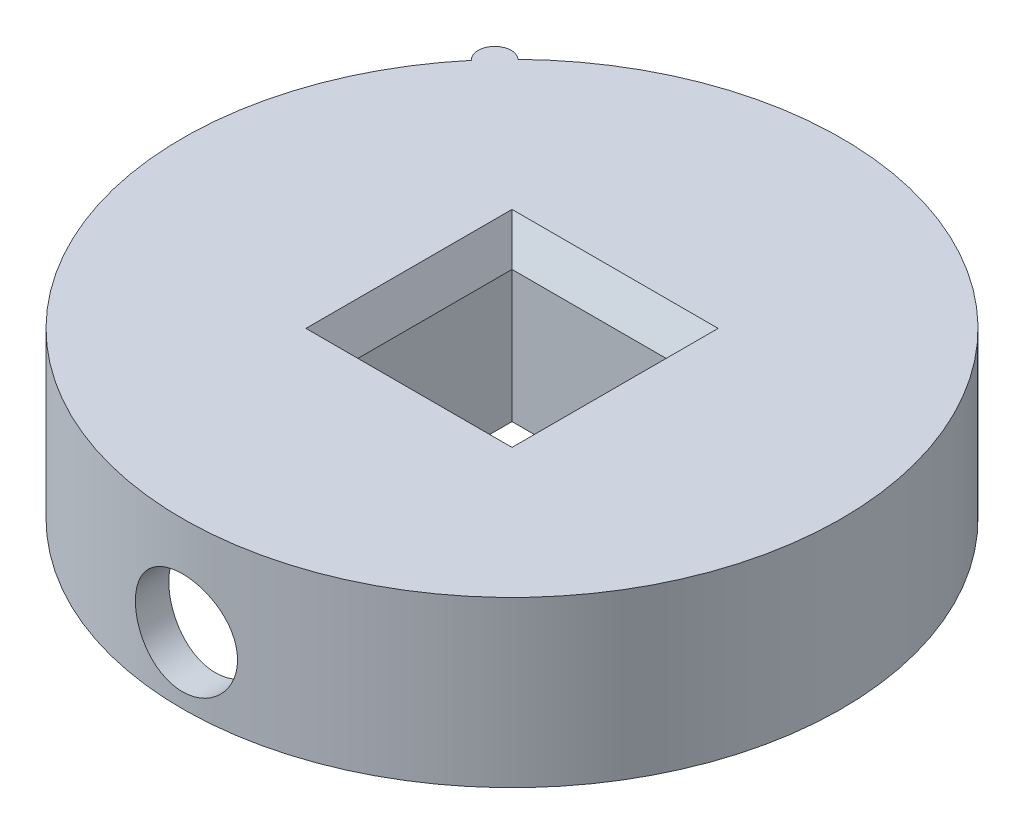
SolidWorks part; units mm, degrees
ref_plane "Спереди" through (0, 0, 0) normal (0, 0, 1) x (1, 0, 0)
ref_plane "Сверху" through (0, 0, 0) normal (0, 1, 0) x (1, 0, 0)
ref_plane "Справа" through (0, 0, 0) normal (1, 0, 0) x (0, 0, -1)
sketch "Sketch1" plane through (0, 0, 0) normal (0, 1, 0) x (1, 0, 0)
  circle A0 centre (0, 0) radius 20
  dimension "D1" = 40
extrude "Boss-Extrude1" add sketch "Sketch1" along normal blind 10
sketch "Sketch2" plane through (0, 0, 0) normal (0, -1, 0) x (1, 0, 0)
  line L1 (5.1, 5.1) -> (-5.1, 5.1)
  line L2 (5.1, 5.1) -> (5.1, -5.1)
  line L3 (5.1, -5.1) -> (-5.1, -5.1)
  line L4 (-5.1, 5.1) -> (-5.1, -5.1)
  line L5 (5.1, 5.1) -> (-5.1, -5.1) construction
  line L6 (5.1, -5.1) -> (-5.1, 5.1) construction
  point P0 (0, 0)
  dimension "D1" = 10.2
extrude "Cut-Extrude2" cut sketch "Sketch2" against normal through all
shell "Shell3" thickness 2
sketch "Sketch3" plane through (0, 0, 7.1) normal (0, 0, 1) x (1, 0, 0)
  line L0 (0, 8) -> (0, 0) construction
  line L1 (7.1, 8) -> (-7.1, 8) construction
  line L2 (7.1, 0) -> (-7.1, 0) construction
  circle A0 centre (0, 4) radius 3.1
  dimension "D1" = 6.2
extrude "Cut-Extrude3" cut sketch "Sketch3" along normal through all
sketch "Sketch4" plane through (0, 10, 0) normal (0, 1, 0) x (1, 0, 0)
  line L0 (0, 0) -> (-20, 0) construction
  line L1 (-20, 0) -> (-15.3209, 12.8558) construction
  line L2 (-15.3209, 12.8558) -> (0, 0) construction
  line L3 (-13.9603, 14.3216) -> (-15.3209, 12.8558)
  circle A0 centre (0, 0) radius 20 construction
  arc A1 (-15.3209, 12.8558) -> (-13.9603, 14.3216) centre (-14.6406, 13.5887) cw
  dimension "D2" = 1
  dimension "D1" = 40
  dimension "D3" = 2
extrude "Boss-Extrude2" add sketch "Sketch4" against normal up to surface (10 mm away) up to face at (0, 0, 18)
chamfer "Chamfer1" distance 2 angle 30 4 edges at (-5.1, 10, 0) (0, 10, 5.1) (5.1, 10, 0) (0, 10, -5.1)
